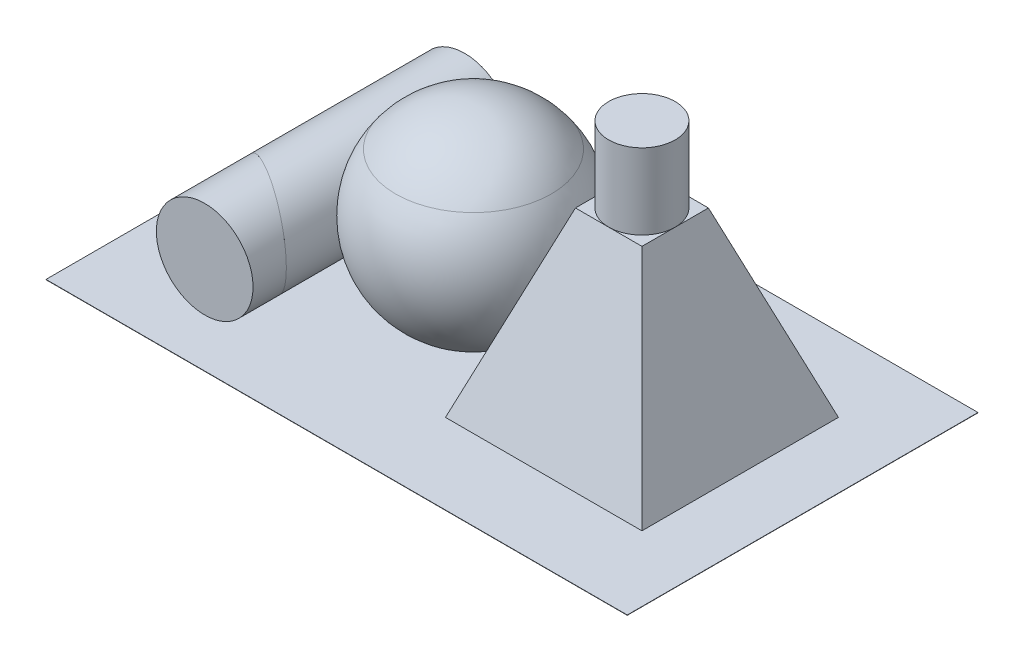
SolidWorks part; units mm, degrees
ref_plane "Front Plane" through (0, 0, 0) normal (0, 0, 1) x (1, 0, 0)
ref_plane "Top Plane" through (0, 0, 0) normal (0, 1, 0) x (1, 0, 0)
ref_plane "Right Plane" through (0, 0, 0) normal (1, 0, 0) x (0, 0, -1)
sketch "Sketch1" plane through (0, 0, 0) normal (0, 0, 1) x (1, 0, 0)
  line L0 (0, 0) -> (65, 0)
  line L1 (65, 0) -> (43.5, 60)
  line L2 (43.5, 60) -> (21.5, 60)
  line L3 (21.5, 60) -> (0, 0)
  line L4 (32.5, 60) -> (32.5, 0) construction
  dimension "D1" = 65
  dimension "D2" = 60
  dimension "D3" = 22
extrude "Boss-Extrude1" add sketch "Sketch1" along normal mid plane 65
sketch "Sketch2" plane through (0, 0, 0) normal (1, 0, 0) x (0, 0, -1)
  line L0 (0, 0) -> (0, 60) construction
  line L1 (-32.5, 60) -> (32.5, 60) construction
  line L2 (11, 60) -> (32.5, 60)
  line L3 (32.5, 60) -> (32.5, 0)
  line L4 (32.5, 0) -> (11, 60)
  line L5 (-32.5, 0) -> (-11, 60)
  line L6 (-32.5, 60) -> (-32.5, 0)
  line L7 (-11, 60) -> (-32.5, 60)
  dimension "D1" = 11
extrude "Cut-Extrude1" cut sketch "Sketch2" along normal through all
sketch "Sketch3" plane through (0, 0, 0) normal (0, 0, 1) x (1, 0, 0)
  line L0 (0, 0) -> (-12.1069, 0) construction
  line L1 (-23.2424, 0) -> (-23.2424, 64) construction
  line L2 (21.5, 60) -> (0, 0) construction
  line L3 (-12.1069, 0) -> (-23.2424, 0)
  line L4 (-23.2424, 49) -> (2.5064, 49)
  line L5 (-23.2424, 0) -> (-23.2424, 49)
  arc A0 (-12.1069, 0) -> (2.5064, 49) centre (-23.2424, 30) ccw
  point P4 (0, 0)
  point P9 (-23.3417, 29.723)
  point P14 (0, 0)
  dimension "D2" = 32
  dimension "D1" = 30
  dimension "D3" = 15
  dimension "D4" = 64
revolve "Revolve1" add sketch "Sketch3" angle 360 about L5
sketch "Sketch4" plane through (0, 0, 0) normal (0, 0, 1) x (1, 0, 0)
  line L0 (-23.2424, 30) -> (-23.2424, 62) construction
  line L1 (-23.2424, 49) -> (2.5064, 49)
  line L2 (-23.2424, 49) -> (-23.2424, 62)
  arc A0 (2.5064, 49) -> (-23.2424, 62) centre (-23.2424, 30) ccw
  dimension "D1" = 32
revolve "Revolve2" add sketch "Sketch4" angle 360 about L2
sketch "Sketch5" plane through (0, 0, 0) normal (0, 0, 1) x (1, 0, 0)
  line L0 (-34.3779, 0) -> (-81.9284, 0) construction
  circle A0 centre (-69.1554, 16) radius 16
  arc A1 (-48.9912, 49) -> (-34.3779, 0) centre (-23.2424, 30) ccw construction
  dimension "D1" = 32
extrude "Boss-Extrude2" add sketch "Sketch5" along normal mid plane 86 separate body
sketch "Sketch6" plane through (0, 0, 0) normal (0, 1, 0) x (1, 0, 0)
  line L0 (-53.1554, 43) -> (-53.1554, -43) construction
  line L1 (-53.1554, -43) -> (-53.1554, 43) construction
  line L2 (-53.1554, -32) -> (-93.6627, -8.6131)
  line L3 (-93.6627, -8.6131) -> (-93.6627, -63.1838)
  line L4 (-93.6627, -63.1838) -> (-40.1544, -61.0613)
  line L5 (-40.1544, -61.0613) -> (-53.1554, -32)
  line L6 (-23.2424, -32) -> (-53.1554, -32) construction
  circle A0 centre (-23.2424, 0) radius 32 construction
  circle A2 centre (-23.2424, 0) radius 32 construction
  dimension "D1" = 60
extrude "Cut-Extrude2" cut sketch "Sketch6" along normal through all
ref_plane "Plane1" through (0, 0, 43) normal (0, 0, 1) x (1, 0, 0)
sketch "Sketch7" plane through (0, 0, 43) normal (0, 0, 1) x (1, 0, 0)
  circle A0 centre (-69.1554, 16) radius 16 construction
  circle A1 centre (-69.1554, 16) radius 16
extrude "Boss-Extrude3" add sketch "Sketch7" against normal up to surface (11 mm away) separate body
sketch "Sketch8" plane through (0, 60, 0) normal (0, 1, 0) x (1, 0, 0)
  line L0 (21.5, 11) -> (43.5, -11) construction
  line L1 (43.5, -11) -> (43.5, 11) construction
  circle A0 centre (32.5, 0) radius 11
extrude "Boss-Extrude4" add sketch "Sketch8" along normal blind 25
sketch "Sketch9" plane through (0, 0, 0) normal (0, 1, 0) x (1, 0, 0)
  line L1 (-105.6109, 56.9919) -> (86.6856, 56.9919)
  line L2 (-105.6109, 56.9919) -> (-105.6109, -59.042)
  line L3 (-105.6109, -59.042) -> (86.6856, -59.042)
  line L4 (86.6856, 56.9919) -> (86.6856, -59.042)
extrude "Boss-Extrude5" add sketch "Sketch9" against normal blind 0.1 separate body
